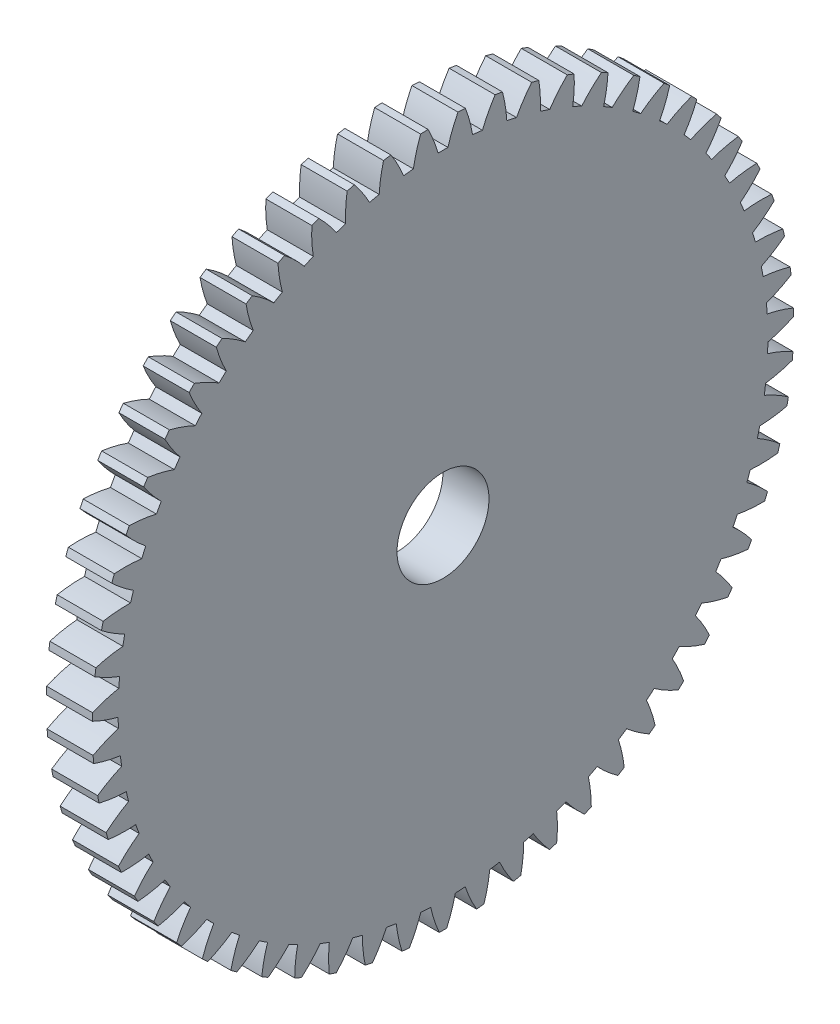
SolidWorks part; units mm, degrees
ref_plane "Plane1" through (0, 0, 0) normal (0, 0, 1) x (1, 0, 0)
ref_plane "Plane2" through (0, 0, 0) normal (0, 1, 0) x (1, 0, 0)
ref_plane "Plane3" through (0, 0, 0) normal (1, 0, 0) x (0, 0, -1)
sketch "HoldingSke" plane through (0, 0, 0) normal (0, 1, 0) x (1, 0, 0)
  line L0 (0, 0) -> (0.515, -0.8572)
  line L1 (-15, 0) -> (100, 0) construction
  line L2 (0, 0) -> (-2.1039, 2.3779)
  line L3 (0, 0) -> (-11.863, 4.5341)
  line L4 (0, 0) -> (4.4479, 7.4025)
  line L5 (0, 0) -> (-46.8476, -17.4728)
  line L6 (0, 0) -> (-3.3159, -2.2372)
  line L7 (-2.1039, 2.3779) -> (8.6586, 51.2059)
  line L8 (-76.2, 54.61) -> (-74.8, 54.61)
  line L9 (-71.009, 38.7566) -> (-53.1078, 45.2721)
  line L10 (-76.2, 71.12) -> (104.1128, 71.12)
  line L11 (0, 0) -> (-4, 0)
  line L12 (-76.2, 101.6) -> (-76.162, 101.6)
  line L13 (24.9733, 27.94) -> (52.9518, 28.4284)
  line L14 (24.9733, 27.94) -> (24.9743, 27.94)
  line L15 (24.9733, 27.94) -> (100.4006, 29.5858)
  line L16 (-63.627, -1) -> (-12.827, -1)
  circle A0 centre (0, 0) radius 4
  circle A1 centre (0, 0) radius 28.249
  circle A2 centre (0, 0) radius 37.5
  circle A3 centre (0, 0) radius 4
  dimension "MHD" = 56.498
  dimension "Hub_dia" = 75
  dimension "Bore" = 8
  dimension "MBD" = 8
  dimension "Num_teeth" = 59
  dimension "Pitch" = 1
  dimension "Overall_len" = 50
  dimension "Show_teeth" = 59
  dimension "Thickness" = 4
  dimension "OAL" = 50.0001
  dimension "T_dim" = 1.4
  dimension "Ap" = 20
  dimension "H" = 19.05
  dimension "Pitch_radius" = 180.3128
  dimension "Width" = 4
  dimension "Backlash" = 0.038
  dimension "Addendum_fac" = 1
  dimension "Dedendum_fac" = 1.25
  dimension "Clearance_fac" = 0.25
  dimension "Dedendum_add" = 0.001
  dimension "Module" = 1
sketch "BasProSke" plane through (0, 0, 0) normal (0, 1, 0) x (1, 0, 0)
  line L0 (-10, 0) -> (60, 0) construction
  line L1 (0, 0) -> (0, 30.5)
  line L2 (0, 0) -> (4, 0)
  line L3 (4, 0) -> (4, 30.5)
  line L4 (4, 30.5) -> (0, 30.5)
  dimension "Thickness" = 4
  dimension "Diameter" = 61
revolve "Base-Revolve" add sketch "BasProSke" angle 360 about L0
sketch "TooCutSke" plane through (0, 0, 0) normal (1, 0, 0) x (0, 0, -1)
  line L1 (0, 0) -> (0, 107) construction
  line L2 (0, 0) -> (-0.8518, 29.4877) construction
  line L3 (0, 0) -> (-3.1392, 58.8989) construction
  line L4 (-0.8518, 29.4877) -> (-1.5696, 29.4494) construction
  arc A0 (0.4308, 28.2457) -> (-0.4308, 28.2457) centre (0, 0) ccw
  arc A1 (1.3141, 30.4971) -> (-1.3141, 30.4971) centre (0, 0) ccw
  circle A2 centre (0, 0) radius 29.5 construction
  circle A3 centre (0, 0) radius 27.7209 construction
  arc A4 (-0.4308, 28.2457) -> (-1.3141, 30.4971) centre (-11.7994, 25.0843) ccw
  arc A5 (1.3141, 30.4971) -> (0.4308, 28.2457) centre (11.7994, 25.0843) ccw
  dimension "Root_dia" = 56.498
  dimension "Overcut_dia" = 61.0508
  dimension "Pitch_dia" = 59
  dimension "Base_dia" = 55.4419
  dimension "Flank_rad" = 11.8
  dimension "Half_ang" = 3.051
  dimension "Half_CT" = 0.7188
extrude "ToothCut" cut sketch "TooCutSke" along normal through all
fillet "Breaks" [suppressed] radius 0.02
fillet "RootFillets" [suppressed] radius 0.251
pattern_circular "TeethCuts" count 59 every 6.102 about axis through (-10, 0, 0) along (1, 0, 0) of "ToothCut", "RootFillets", "Breaks"
sketch "HubNeaOneSke" plane through (0, 0, 0) normal (-1, 0, 0) x (0, 0, 1)
  circle A0 centre (0, 0) radius 28.249
  dimension "Diameter" = 56.498
extrude "HubNearOne" [suppressed] add sketch "HubNeaOneSke" along normal blind 46.0001
sketch "HubNeaBotSke" plane through (0, 0, 0) normal (-1, 0, 0) x (0, 0, 1)
  circle A0 centre (0, 0) radius 28.249
  dimension "Diameter" = 56.498
extrude "HubNearBoth" [suppressed] add sketch "HubNeaBotSke" along normal blind 23
ref_plane "FarPln" through (4, 0, 0) normal (1, 0, 0) x (0, 0, -1)
sketch "HubFarSke" plane through (4, 0, 0) normal (1, 0, 0) x (0, 0, -1)
  circle A0 centre (0, 0) radius 28.249
  dimension "Diameter" = 56.498
extrude "HubFar" [suppressed] add sketch "HubFarSke" along normal blind 23
sketch "BorSke" plane through (0, 0, 0) normal (1, 0, 0) x (0, 0, -1)
  circle A0 centre (0, 0) radius 4
  dimension "Diameter" = 8
extrude "Bore" cut sketch "BorSke" along normal mid plane 100.0001
sketch "KeySke" plane through (0, 0, 0) normal (1, 0, 0) x (0, 0, -1)
  line L0 (-1.5, 0) -> (-1.5, 5.4)
  line L1 (-1.5, 5.4) -> (1.5, 5.4)
  line L2 (1.5, 5.4) -> (1.5, 0)
  line L3 (0, 0) -> (0, 34) construction
  line L4 (-1.5, 0) -> (1.5, 0)
  dimension "Offset" = 5.4
  dimension "Width" = 3
extrude "Keyway" [suppressed] cut sketch "KeySke" along normal mid plane 100.0001
pattern_circular "Keyway2" [suppressed] count 2 every 90 about axis through (-10, 0, 0) along (1, 0, 0)
equation "' \"Module@HoldingSke\" = 6.35"
equation "' \"Num_teeth@HoldingSke\" = 12"
equation "' \"Ap@HoldingSke\" =  20"
equation "' \"Ap@HoldingSke\" = 20"
equation "' \"Width@HoldingSke\" = 0.5 * 25.4"
equation "' \"Hub_dia@HoldingSke\"= 1 * 25.4"
equation "' \"Hub_dia@HoldingSke\" = 1 * 25.4"
equation "' \"Overall_len@HoldingSke\" = 1.0 * 25.4"
equation "' \"Bore@HoldingSke\" = 0.75 * 25.4"
equation "' \"T_dim@HoldingSke\" = 0.1 * 25.4"
equation "' \"Width@KeySke\" = 0.25 * 25.4"
equation "' \"Show_teeth@HoldingSke\" = 13"
equation "' \"Backlash@HoldingSke\" = 0.009 * 25.4"
equation "' \"Addendum_fac@HoldingSke\" = 1.0"
equation "' \"Dedendum_fac@HoldingSke\" = 1.25"
equation "' \"Dedendum_add@HoldingSke\" = 0.00005 * 25.4"
equation "' \"Clearance_fac@HoldingSke\" = 0.25"
equation "\"Pitch@HoldingSke\" = 1 / \"Module@HoldingSke\""
equation "\"Overcut_dia@TooCutSke\" = (\"Num_teeth@HoldingSke\" + 2 * \"Addendum_fac@HoldingSke\") / \"Pitch@HoldingSke\" + 0.002 * 25.4"
equation "\"Pitch_dia@TooCutSke\" = \"Num_teeth@HoldingSke\" / \"Pitch@HoldingSke\""
equation "\"Base_dia@TooCutSke\" = \"Num_teeth@HoldingSke\" / \"Pitch@HoldingSke\" * cos((\"Ap@HoldingSke\"  * 3.14159265 / 180))"
equation "\"Root_dia@TooCutSke\" = (\"Num_teeth@HoldingSke\" + 2) / \"Pitch@HoldingSke\" - 2 * (\"Addendum_fac@HoldingSke\" + \"Dedendum_fac@HoldingSke\") / \"Pitch@HoldingSke\" - \"Dedendum_add@HoldingSke\" * 2"
equation "\"Half_ang@TooCutSke\" = 180 / \"Num_teeth@HoldingSke\""
equation "\"Half_CT@TooCutSke\" = \"Num_teeth@HoldingSke\" / \"Pitch@HoldingSke\" * sin((3.14159265 / 2 / \"Num_teeth@HoldingSke\")) / 2 - 7 * \"Backlash@HoldingSke\" / 4"
equation "\"Flank_rad@TooCutSke\" = \"Num_teeth@HoldingSke\" / \"Pitch@HoldingSke\" / 5"
equation "\"Radius@RootFillets\" = \"Clearance_fac@HoldingSke\" / \"Pitch@HoldingSke\" + \"Dedendum_add@HoldingSke\""
equation "\"Break_rad@Breaks\" = 0.02 / \"Pitch@HoldingSke\""
equation "\"Thickness@HoldingSke\" = \"Width@HoldingSke\""
equation "\"OAL@HoldingSke\" = \"Thickness@HoldingSke\""
equation "\"MHD@HoldingSke\" = (\"Num_teeth@HoldingSke\" + 2) / \"Pitch@HoldingSke\" - 2 * (\"Addendum_fac@HoldingSke\" + \"Dedendum_fac@HoldingSke\")  / \"Pitch@HoldingSke\" - \"Dedendum_add@HoldingSke\" * 2"
equation "\"MBD@HoldingSke\" = (\"Num_teeth@HoldingSke\" + 2) / \"Pitch@HoldingSke\" - 2 * (\"Addendum_fac@HoldingSke\" + \"Dedendum_fac@HoldingSke\")  / \"Pitch@HoldingSke\" - \"Dedendum_add@HoldingSke\" * 2 - 0.002 * 25.4"
equation "\"MHD@HoldingSke\" = ((sgn( \"MHD@HoldingSke\" - \"Hub_dia@HoldingSke\" )-1)*( \"MHD@HoldingSke\" - \"Hub_dia@HoldingSke\" ))/-2+ \"Hub_dia@HoldingSke\""
equation "\"MBD@HoldingSke\" = ((sgn( \"MBD@HoldingSke\" - \"Bore@HoldingSke\" )-1)*( \"MBD@HoldingSke\" - \"Bore@HoldingSke\" ))/-2+ \"Bore@HoldingSke\""
equation "\"OAL@HoldingSke\" = ((sgn( \"OAL@HoldingSke\" - \"Overall_len@HoldingSke\" )+1)*( \"OAL@HoldingSke\" - \"Overall_len@HoldingSke\" ))/2 + \"Overall_len@HoldingSke\" + 0.000002 * 25.4"
equation "\"Num_teeth@TeethCuts\" = int( \"Show_teeth@HoldingSke\" ) + 1"
equation "\"Num_teeth@TeethCuts\" = ((sgn( \"Num_teeth@TeethCuts\" - \"Num_teeth@HoldingSke\" )-1)*( \"Num_teeth@TeethCuts\" - \"Num_teeth@HoldingSke\" ))/-2+ \"Num_teeth@HoldingSke\""
equation "\"Num_teeth@TeethCuts\" = ((sgn( \"Num_teeth@TeethCuts\" - 2.0)+1)*( \"Num_teeth@TeethCuts\" - 2.0))/2 +2.0"
equation "\"Angle@TeethCuts\" = 360.0 / \"Num_teeth@HoldingSke\""
equation "\"Diameter@BasProSke\" = (\"Num_teeth@HoldingSke\" + 2 * \"Addendum_fac@HoldingSke\") / \"Pitch@HoldingSke\""
equation "\"Thickness@BasProSke\"  = \"Thickness@HoldingSke\""
equation "' \"Fillet_rad@BasProSke\" =  \"Thickness@HoldingSke\" * 0.05"
equation "' \"Fillet_rad@BasProSke\" = \"Thickness@HoldingSke\" * 0.05"
equation "\"MHD@HoldingSke\" = ((sgn( \"MHD@HoldingSke\" - \"Root_dia@TooCutSke\" )-1)*( \"MHD@HoldingSke\" - \"Root_dia@TooCutSke\" ))/-2+ \"Root_dia@TooCutSke\""
equation "\"Diameter@HubNeaOneSke\" = \"MHD@HoldingSke\""
equation "\"Length@HubNearOne\" = \"OAL@HoldingSke\" - \"Thickness@BasProSke\""
equation "\"Diameter@HubNeaBotSke\" = \"MHD@HoldingSke\""
equation "\"Length@HubNearBoth\" = ( \"OAL@HoldingSke\" - \"Thickness@BasProSke\" ) / 2.0"
equation "\"Thickness@FarPln\" = \"Thickness@BasProSke\""
equation "\"Diameter@HubFarSke\" = \"MHD@HoldingSke\""
equation "\"Length@HubFar\" = ( \"OAL@HoldingSke\" - \"Thickness@BasProSke\" ) / 2.0"
equation "\"Diameter@BorSke\" = \"MBD@HoldingSke\""
equation "\"D1@Bore\" = \"OAL@HoldingSke\" * 2.0"
equation "\"D1@Keyway\" = \"OAL@HoldingSke\" * 2.0"
equation "\"Offset@KeySke\" = \"T_dim@HoldingSke\" + \"MBD@HoldingSke\" / 2.0"
